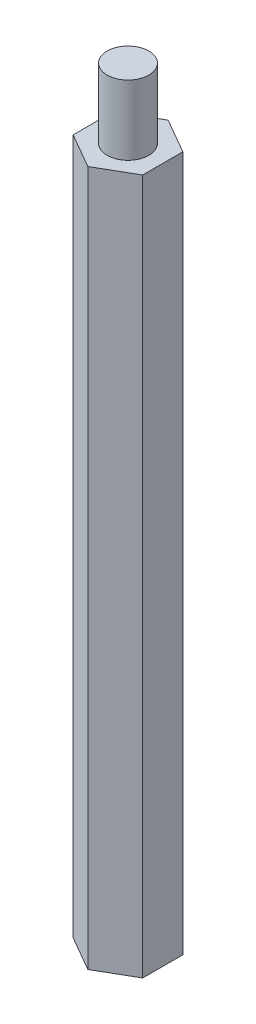
SolidWorks part; units mm, degrees
ref_plane "Front Plane" through (0, 0, 0) normal (0, 0, 1) x (1, 0, 0)
ref_plane "Top Plane" through (0, 0, 0) normal (0, 1, 0) x (1, 0, 0)
ref_plane "Right Plane" through (0, 0, 0) normal (1, 0, 0) x (0, 0, -1)
sketch "Sketch1" plane through (0, 0, 0) normal (0, 1, 0) x (1, 0, 0)
  line L1 (0, -5.7735) -> (5, -2.8868)
  line L2 (5, -2.8868) -> (5, 2.8868)
  line L3 (5, 2.8868) -> (0, 5.7735)
  line L4 (0, 5.7735) -> (-5, 2.8868)
  line L5 (-5, 2.8868) -> (-5, -2.8868)
  line L6 (-5, -2.8868) -> (0, -5.7735)
  circle A0 centre (0, 0) radius 5 construction
  dimension "D1" = 10
extrude "Boss-Extrude1" add sketch "Sketch1" along normal blind 100
sketch "Sketch2" plane through (0, 100, 0) normal (0, 1, 0) x (1, 0, 0)
  circle A0 centre (0, 0) radius 3
  dimension "D1" = 6
extrude "Boss-Extrude2" add sketch "Sketch2" along normal blind 10
sketch "Sketch3" plane through (0, 0, 0) normal (0, -1, 0) x (1, 0, 0)
  circle A0 centre (0, 0) radius 3
  dimension "D1" = 6
extrude "Cut-Extrude1" cut sketch "Sketch3" against normal blind 12
